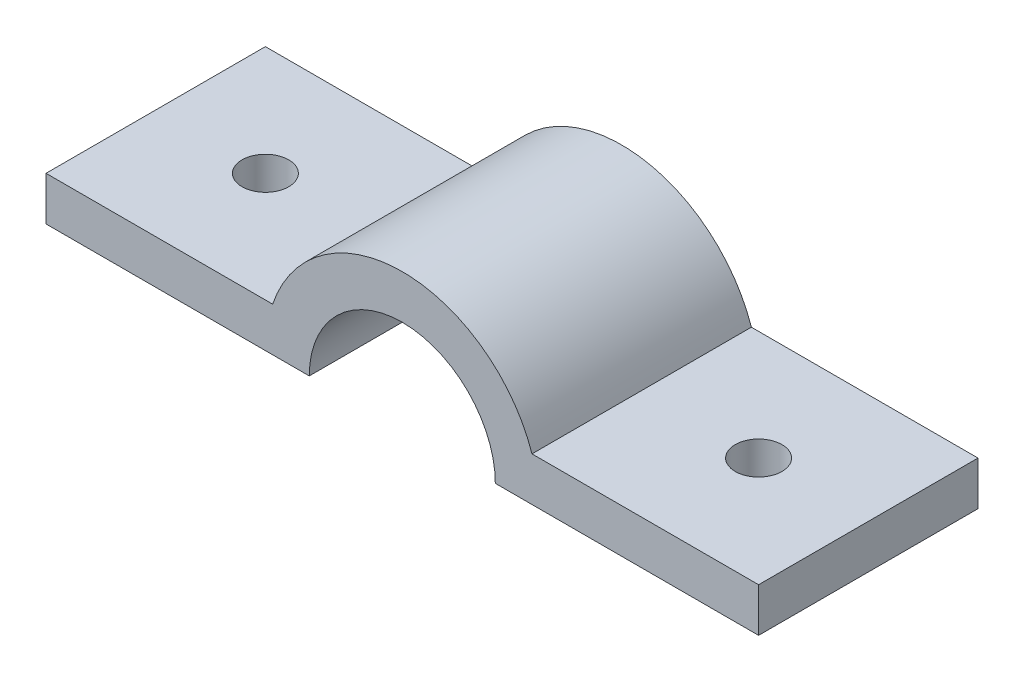
SolidWorks part; units mm, degrees
ref_plane "Front Plane" through (0, 0, 0) normal (0, 0, 1) x (1, 0, 0)
ref_plane "Top Plane" through (0, 0, 0) normal (0, 1, 0) x (1, 0, 0)
ref_plane "Right Plane" through (0, 0, 0) normal (1, 0, 0) x (0, 0, -1)
sketch "Sketch1" plane through (0, 0, 0) normal (0, 0, 1) x (1, 0, 0)
  line L21 (32.7952, 6.35) -> (0, 6.35)
  line L22 (0, 6.35) -> (0, 0)
  line L23 (0, 0) -> (38.1, 0)
  line L25 (70.3288, 6.35) -> (103.124, 6.35)
  line L26 (103.124, 6.35) -> (103.124, 0)
  line L27 (103.124, 0) -> (65.024, 0)
  arc A2 (38.1, 0) -> (65.024, 0) centre (51.562, 0) cw
  arc A4 (32.7952, 6.35) -> (70.3288, 6.35) centre (51.562, 0) cw
  point P6 (51.562, 13.462)
  dimension "D1" = 6.35
  dimension "D2" = 103.124
  dimension "D4" = 6.35
  dimension "D5" = 38.1
  dimension "D3" = 13.462
  dimension "D6" = 19.812
  dimension "D7" = 13.462
extrude "Boss-Extrude1" add sketch "Sketch1" along normal blind 31.75
sketch "Sketch3" plane through (0, 6.35, 0) normal (0, 1, 0) x (1, 0, 0)
  line L5 (32.7952, -31.75) -> (0, -31.75) construction
  line L6 (103.124, -31.75) -> (70.3288, -31.75) construction
  line L10 (0, -31.75) -> (0, 0) construction
  line L11 (103.124, -31.75) -> (103.124, 0) construction
  circle A2 centre (15.875, -15.875) radius 3.3782
  circle A3 centre (87.249, -15.875) radius 3.3782
  dimension "D1" = 6.7564
  dimension "D2" = 6.7564
  dimension "D3" = 15.875
  dimension "D4" = 15.875
  dimension "D5" = 15.875
  dimension "D6" = 15.875
extrude "Cut-Extrude1" cut sketch "Sketch3" against normal through all
